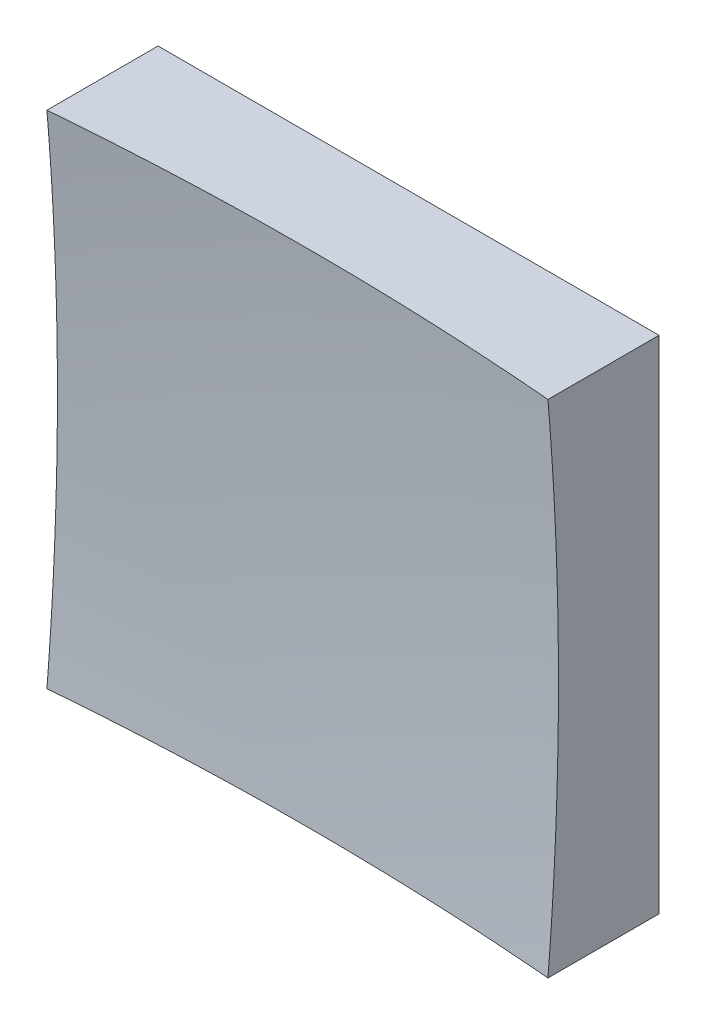
SolidWorks part; units mm, degrees
ref_plane "前视基准面" through (0, 0, 0) normal (0, 0, 1) x (1, 0, 0)
ref_plane "上视基准面" through (0, 0, 0) normal (0, 1, 0) x (1, 0, 0)
ref_plane "右视基准面" through (0, 0, 0) normal (1, 0, 0) x (0, 0, -1)
sketch "草图1" plane through (0, 0, 0) normal (0, 0, 1) x (1, 0, 0)
  line L1 (-25, 25) -> (25, 25)
  line L2 (-25, 25) -> (-25, -25)
  line L3 (-25, -25) -> (25, -25)
  line L4 (25, 25) -> (25, -25)
  line L5 (-25, 25) -> (25, -25) construction
  line L6 (-25, -25) -> (25, 25) construction
  point P0 (0, 0)
  dimension "D1" = 50
  dimension "D2" = 50
extrude "凸台-拉伸1" add sketch "草图1" along normal blind 50 contours L2 L3 L4 L1
sketch "草图2" plane through (0, 0, 0) normal (0, 1, 0) x (1, 0, 0)
  line L0 (-7.4603, -9) -> (7.3192, -9) construction
  line L1 (0, 0) -> (0, -12.1749) construction
  line L2 (292.4536, -242.1354) -> (0, -242.1354)
  line L3 (0, -242.1354) -> (0, -9)
  arc A1 (292.4536, -242.1354) -> (0, -9) centre (0, -309) ccw
  dimension "D2" = 600
  dimension "D1" = 9
revolve "切除-旋转2" cut sketch "草图2" angle 360 about L3
